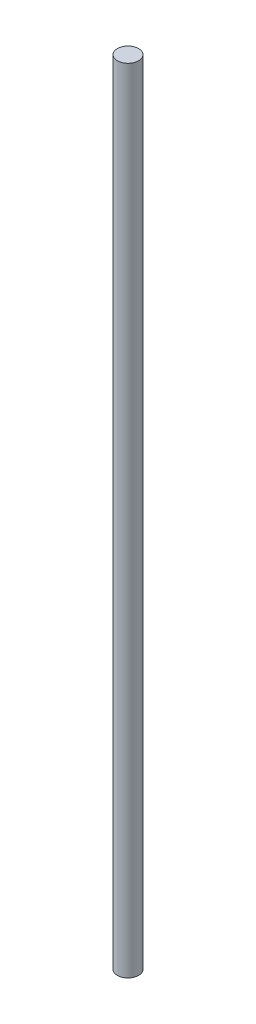
SolidWorks part; units mm, degrees
ref_plane "Front Plane" through (0, 0, 0) normal (0, 0, 1) x (1, 0, 0)
ref_plane "Top Plane" through (0, 0, 0) normal (0, 1, 0) x (1, 0, 0)
ref_plane "Right Plane" through (0, 0, 0) normal (1, 0, 0) x (0, 0, -1)
sketch "Sketch1" plane through (0, 0, 0) normal (0, 1, 0) x (1, 0, 0)
  circle A0 centre (0, 0) radius 2.3813
  dimension "D1" = 4.7625
extrude "Boss-Extrude1" add sketch "Sketch1" along normal blind 177.8
